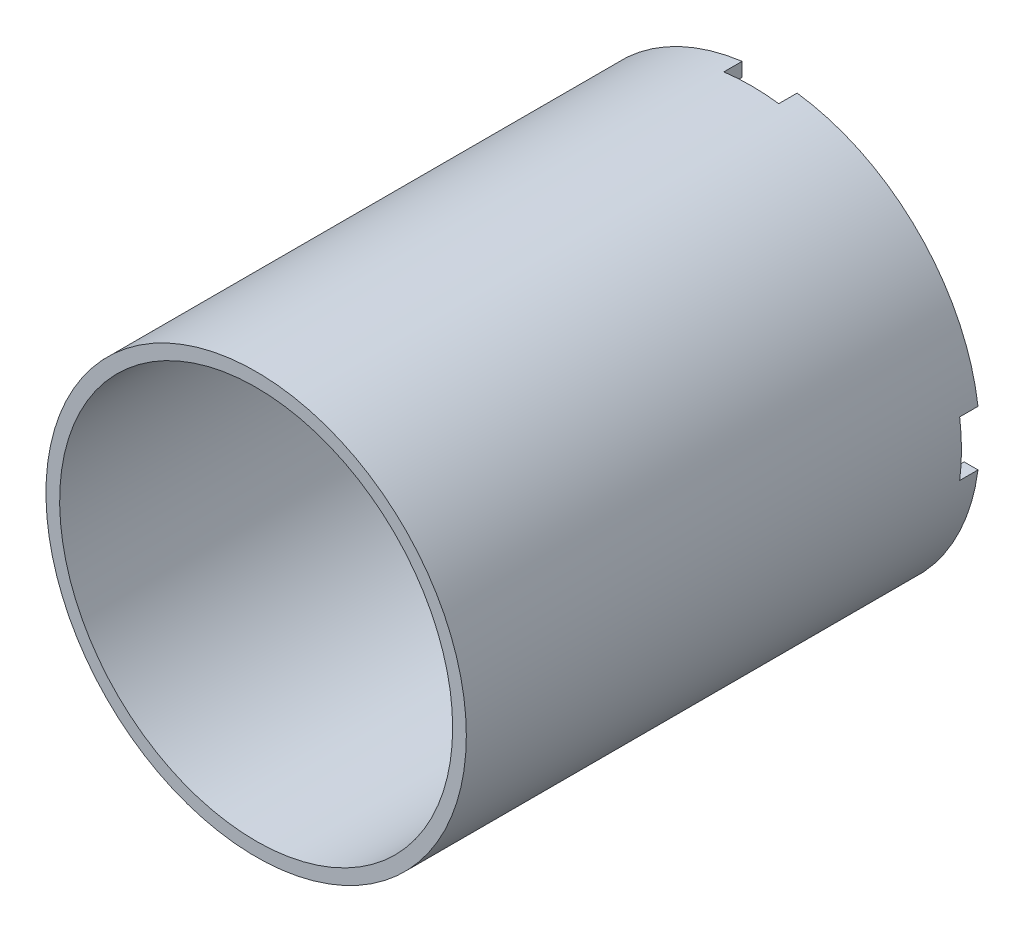
SolidWorks part; units mm, degrees
material "A-Glass Fiber"
ref_plane "Ebene vorne" through (0, 0, 0) normal (0, 0, 1) x (1, 0, 0)
ref_plane "Ebene oben" through (0, 0, 0) normal (0, 1, 0) x (1, 0, 0)
ref_plane "Ebene rechts" through (0, 0, 0) normal (1, 0, 0) x (0, 0, -1)
sketch "Sketch1" plane through (0, 0, 0) normal (0, 0, 1) x (1, 0, 0)
  circle A0 centre (0, 0) radius 42.8625
  circle A1 centre (0, 0) radius 45.847
  dimension "D1" = 85.725
  dimension "D2" = 91.694
extrude "Boss-Extrude1" add sketch "Sketch1" along normal blind 112 contours A0 | A1
ref_plane "Plane1" through (-45.847, 0, 0) normal (-1, 0, 0) x (0, 0, 1)
sketch "Sketch2" plane through (-45.847, 0, 0) normal (-1, 0, 0) x (0, 0, 1)
  line L0 (0, 45.847) -> (0, -45.847) construction
  circle A0 centre (9, 0) radius 0.75
  dimension "D1" = 9
  dimension "D2" = 1.5
sketch "Sketch3" plane through (0, 0, 0) normal (0, 0, -1) x (-1, 0, 0)
  line L0 (0, 45.847) -> (0, -45.847) construction
  line L1 (0, 0) -> (-45.847, 0) construction
  line L2 (6, 45.847) -> (-6, 45.847)
  line L3 (-6, 45.847) -> (-6, 6)
  line L4 (-6, 6) -> (-45.847, 6)
  line L5 (-45.847, 6) -> (-45.847, -6)
  line L6 (45.847, 6) -> (45.847, -6)
  line L7 (6, 6) -> (45.847, 6)
  line L8 (6, 45.847) -> (6, 6)
  line L9 (6, -45.847) -> (6, -6)
  line L10 (6, -6) -> (45.847, -6)
  line L11 (-6, -6) -> (-45.847, -6)
  line L12 (-6, -45.847) -> (-6, -6)
  line L13 (6, -45.847) -> (-6, -45.847)
  circle A0 centre (0, 0) radius 45.847 construction
  point P20 (45.847, 0)
  dimension "D1" = 6
  dimension "D2" = 6
extrude "Cut-Extrude1" cut sketch "Sketch3" against normal blind 4
